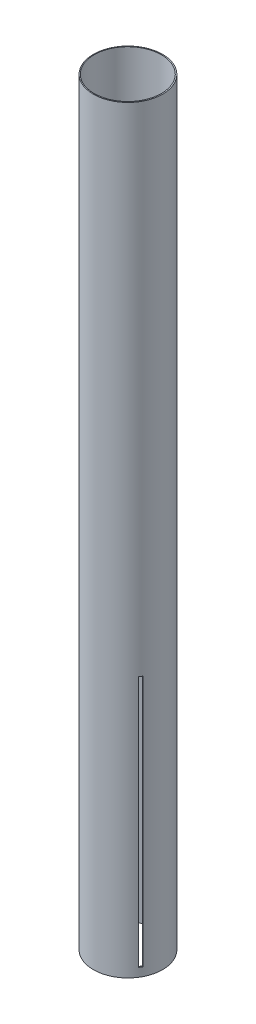
SolidWorks part; units mm, degrees
ref_plane "Front Plane" through (0, 0, 0) normal (0, 0, 1) x (1, 0, 0)
ref_plane "Top Plane" through (0, 0, 0) normal (0, 1, 0) x (1, 0, 0)
ref_plane "Right Plane" through (0, 0, 0) normal (1, 0, 0) x (0, 0, -1)
sketch "Sketch1" plane through (0, 0, 0) normal (0, 1, 0) x (1, 0, 0)
  circle A0 centre (0, 0) radius 51
  circle A1 centre (-0.3423, 0) radius 49.55
  dimension "D1" = 102
  dimension "D2" = 99.1
extrude "Boss-Extrude1" add sketch "Sketch1" along normal blind 1117.6
sketch "Sketch2" plane through (0, 0, 0) normal (0, 0, 1) x (1, 0, 0)
  line L0 (0, 12.7) -> (2.38, 12.7)
  line L1 (2.38, 12.7) -> (2.38, 383.7)
  line L2 (2.38, 383.7) -> (-2.38, 383.7)
  line L3 (-2.38, 383.7) -> (-2.38, 12.7)
  line L4 (-2.38, 12.7) -> (0, 12.7)
  line L5 (0, 1117.6) -> (0, 0) construction
  line L6 (-51, 0) -> (51, 0) construction
  dimension "D1" = 4.76
  dimension "D2" = 2.38
  dimension "D3" = 0
  dimension "D4" = 371
  dimension "D5" = 12.7
extrude "Cut-Extrude1" cut sketch "Sketch2" against normal through all
pattern_circular "CirPattern1" count 3 over 360 about axis through (0, 0, 0) along (0, 1, 0) of "Cut-Extrude1"
